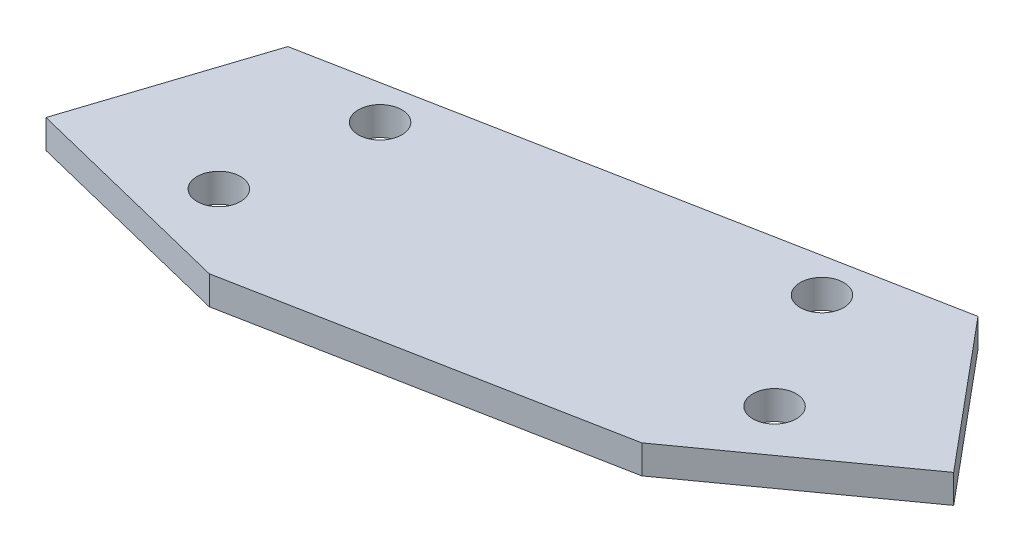
SolidWorks part; units mm, degrees
material "Thornel Mat VMA"
ref_plane "前视基准面" through (0, 0, 0) normal (0, 0, 1) x (1, 0, 0)
ref_plane "上视基准面" through (0, 0, 0) normal (0, 1, 0) x (1, 0, 0)
ref_plane "右视基准面" through (0, 0, 0) normal (1, 0, 0) x (0, 0, -1)
other "Configuration Table"
sketch "草图2" plane through (0, 0, 0) normal (0, 1, 0) x (1, 0, 0)
  line L0 (117.1333, 13.6532) -> (157.5965, 21.4408)
  line L1 (157.5965, 21.4408) -> (166.1917, 11.145)
  line L2 (166.1917, 11.145) -> (153.4992, 2.0303)
  line L3 (153.4992, 2.0303) -> (128.1425, -2.8499)
  line L4 (128.1425, -2.8499) -> (112.9736, 0.9025)
  line L5 (112.9736, 0.9025) -> (117.1333, 13.6532)
  circle A0 centre (124.9428, 12.2925) radius 1.52
  circle A1 centre (123.343, 2.6143) radius 1.52
  circle A2 centre (150.8499, 17.2786) radius 1.52
  circle A3 centre (155.9277, 8.8856) radius 1.52
extrude "凸台-拉伸2" add sketch "草图2" along normal blind 2
